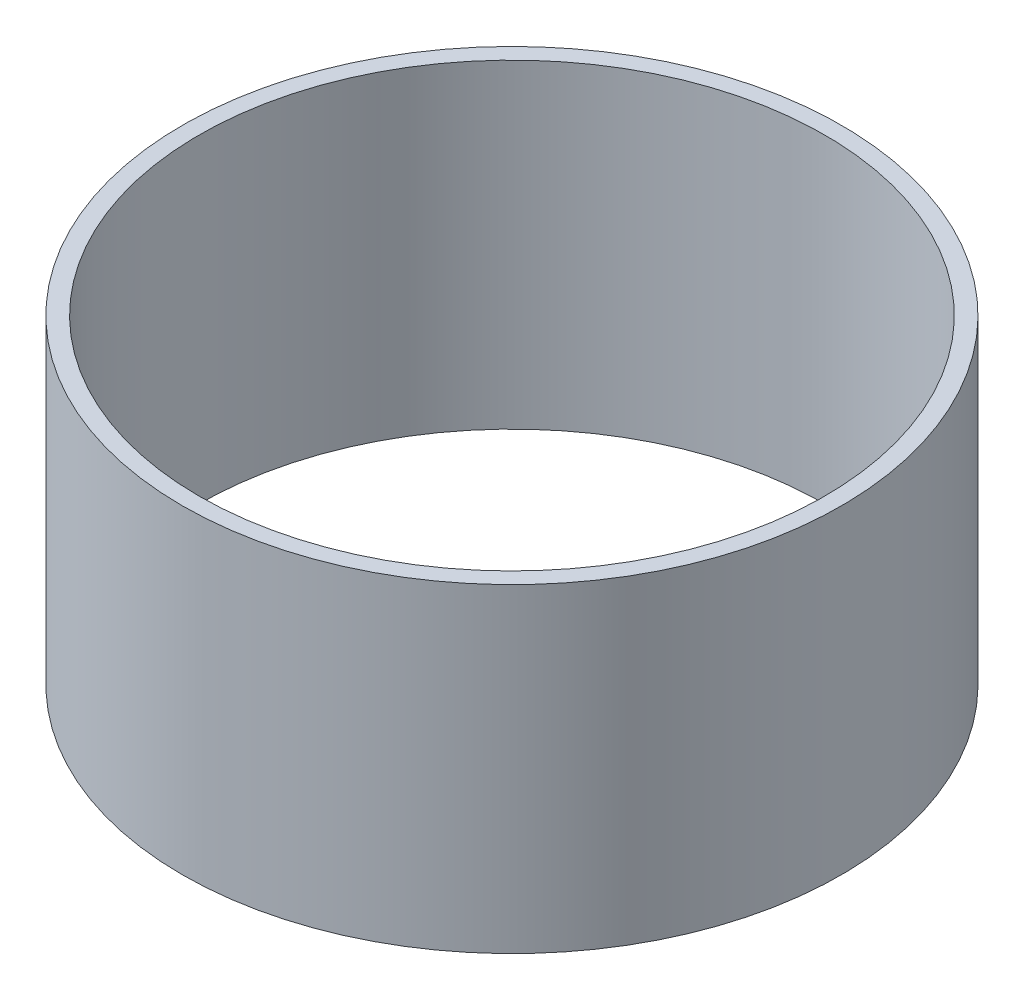
SolidWorks part; units mm, degrees
material "PVC Rigid"
ref_plane "Front Plane" through (0, 0, 0) normal (0, 0, 1) x (1, 0, 0)
ref_plane "Top Plane" through (0, 0, 0) normal (0, 1, 0) x (1, 0, 0)
ref_plane "Right Plane" through (0, 0, 0) normal (1, 0, 0) x (0, 0, -1)
sketch "Sketch1" plane through (0, 0, 0) normal (0, 1, 0) x (1, 0, 0)
  circle A0 centre (0, 0) radius 93.6625
  circle A1 centre (0, 0) radius 88.9
  dimension "D1" = 187.325
  dimension "D2" = 177.8
extrude "Boss-Extrude1" add sketch "Sketch1" along normal mid plane 90.8152
